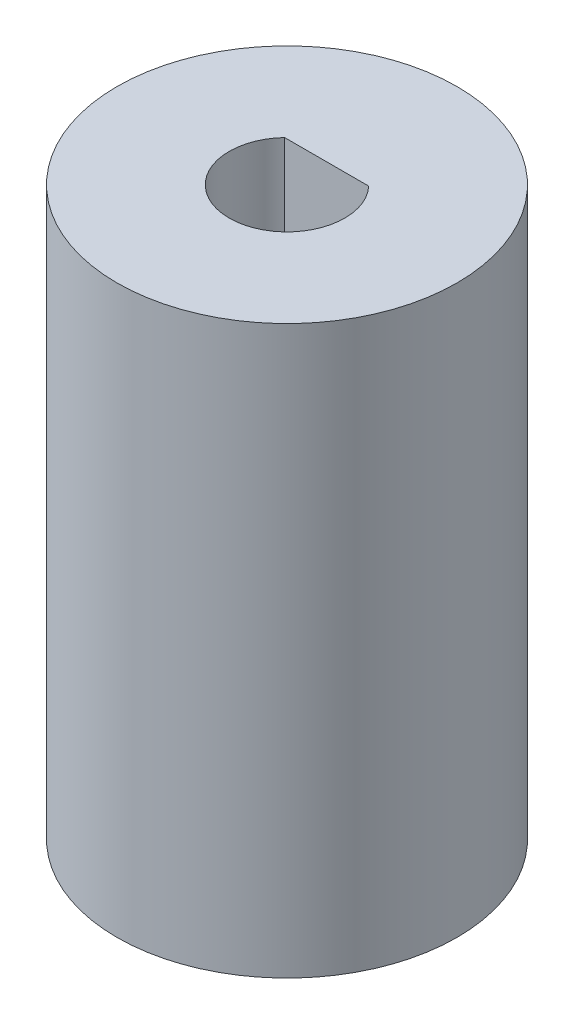
SolidWorks part; units mm, degrees
ref_plane "Front Plane" through (0, 0, 0) normal (0, 0, 1) x (1, 0, 0)
ref_plane "Top Plane" through (0, 0, 0) normal (0, 1, 0) x (1, 0, 0)
ref_plane "Right Plane" through (0, 0, 0) normal (1, 0, 0) x (0, 0, -1)
sketch "Sketch1" plane through (0, 0, 0) normal (0, 1, 0) x (1, 0, 0)
  circle A0 centre (0, 0) radius 15
  dimension "D1" = 30
extrude "Boss-Extrude1" add sketch "Sketch1" along normal blind 50
sketch "Sketch2" plane through (0, 50, 0) normal (0, 1, 0) x (1, 0, 0)
  line L0 (-3.7094, 3.5) -> (3.7094, 3.5)
  line L1 (-5.1, -5.1) -> (5.1, -5.1) construction
  arc A0 (-3.7094, 3.5) -> (3.7094, 3.5) centre (0, 0) ccw
  dimension "D1" = 10.2
  dimension "D2" = 8.6
extrude "Cut-Extrude1" cut sketch "Sketch2" against normal blind 20
sketch "Sketch3" plane through (0, 0, 0) normal (0, -1, 0) x (1, 0, 0)
  line L0 (-8.589, 0) -> (8.566, 0) construction
  line L1 (0, 0) -> (-4.7624, 8.2487) construction
  line L2 (0, 0) -> (4.975, 8.6169) construction
  line L3 (-6.5, 0) -> (-3.25, 5.6292)
  line L4 (-3.25, 5.6292) -> (3.25, 5.6292)
  line L5 (3.25, 5.6292) -> (6.5, 0)
  line L6 (3.25, -5.6292) -> (6.5, 0)
  line L7 (-3.25, -5.6292) -> (3.25, -5.6292)
  line L8 (-6.5, 0) -> (-3.25, -5.6292)
  circle A0 centre (0, 0) radius 6.5
  dimension "D1" = 13
  dimension "D2" = 60
  dimension "D3" = 60
extrude "Cut-Extrude2" cut sketch "Sketch3" against normal blind 30 contours L3 L8 L7 L6 L5 L4
